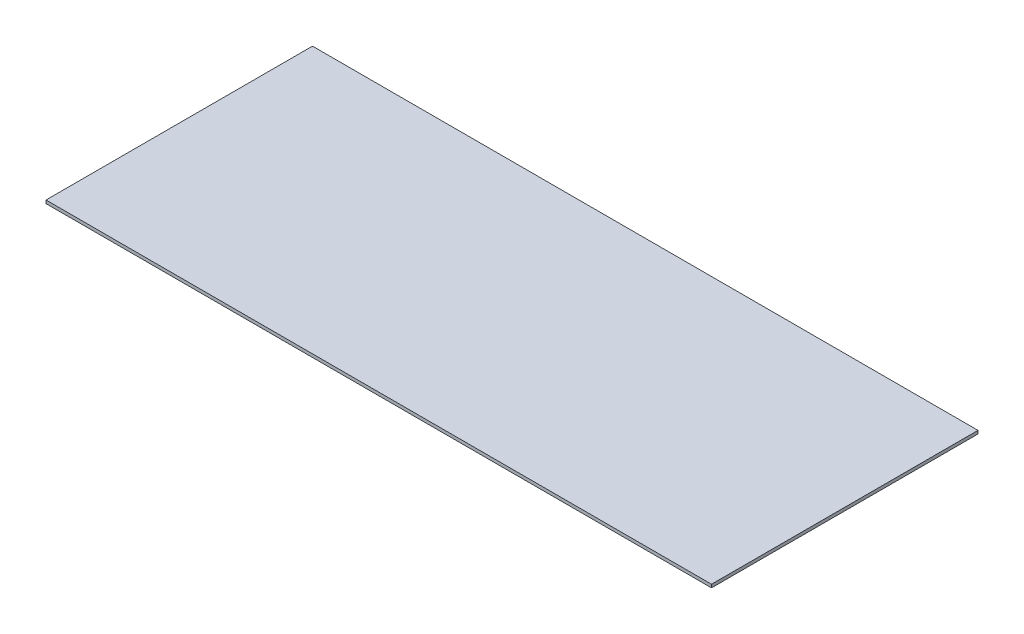
SolidWorks part; units mm, degrees
ref_plane "Front Plane" through (0, 0, 0) normal (0, 0, 1) x (1, 0, 0)
ref_plane "Top of Plywood" through (0, 0, 0) normal (0, 1, 0) x (1, 0, 0)
ref_plane "Right Plane" through (0, 0, 0) normal (1, 0, 0) x (0, 0, -1)
sketch "Interior Dim" plane through (0, 0, 0) normal (0, 1, 0) x (1, 0, 0)
  line L1 (0, 0) -> (5867.4, 0)
  line L2 (0, 0) -> (0, 2349.5)
  line L3 (0, 2349.5) -> (5867.4, 2349.5)
  line L4 (5867.4, 0) -> (5867.4, 2349.5)
  dimension "D1" = 5867.4
  dimension "D2" = 2349.5
sketch "Stud Centerlines" plane through (0, 0, 0) normal (0, 1, 0) x (1, 0, 0)
  line L0 (19.05, 19.05) -> (19.05, 2330.45) construction
  line L1 (19.05, 2330.45) -> (5867.4, 2330.45) construction
  line L2 (5867.4, 0) -> (5867.4, 2349.5) construction
  line L3 (5867.4, 19.05) -> (19.05, 19.05) construction
  line L4 (0, 0) -> (0, 2349.5) construction
  line L5 (0, 2349.5) -> (5867.4, 2349.5) construction
  line L6 (0, 0) -> (5867.4, 0) construction
  line L8 (4121.15, 2330.45) -> (4121.15, 19.05) construction
  line L9 (1771.65, 2330.45) -> (1771.65, 19.05) construction
  line L10 (19.05, 2051.05) -> (4121.15, 2051.05) construction
  dimension "D1" = 19.05
  dimension "D2" = 19.05
  dimension "D3" = 19.05
  dimension "D5" = 279.4
  dimension "D6" = 1752.6
  dimension "D7" = 2349.5
sketch "Gypsum Board" plane through (0, 0, 0) normal (0, 1, 0) x (1, 0, 0)
  line L0 (38.1, 38.1) -> (38.1, 2311.4)
  line L1 (38.1, 2311.4) -> (5867.4, 2311.4)
  line L2 (5867.4, 0) -> (5867.4, 2349.5) construction
  line L3 (50.8, 2298.7) -> (50.8, 50.8)
  line L4 (38.1, 38.1) -> (5867.4, 38.1)
  line L5 (50.8, 50.8) -> (5867.4, 50.8)
  line L6 (19.05, 19.05) -> (19.05, 2330.45) construction
  line L7 (19.05, 2330.45) -> (5867.4, 2330.45) construction
  line L8 (5867.4, 19.05) -> (19.05, 19.05) construction
  line L9 (4165.6, 50.8) -> (4165.6, 2095.5)
  line L10 (50.8, 2298.7) -> (5867.4, 2298.7)
  line L11 (4165.6, 2095.5) -> (4178.3, 2095.5)
  line L12 (4178.3, 2095.5) -> (4178.3, 50.8)
  line L13 (4121.15, 2330.45) -> (4121.15, 19.05) construction
  line L14 (19.05, 2051.05) -> (4121.15, 2051.05) construction
  line L15 (5867.4, 2311.4) -> (5867.4, 2298.7)
  line L16 (5867.4, 50.8) -> (5867.4, 38.1)
  line L17 (4165.6, 50.8) -> (4178.3, 50.8)
  dimension "D1" = 19.05
  dimension "D2" = 19.05
  dimension "D3" = 12.7
  dimension "D4" = 12.7
  dimension "D5" = 12.7
  dimension "D6" = 19.05
  dimension "D7" = 44.45
  dimension "D8" = 12.7
  dimension "D9" = 44.45
sketch "PVC" plane through (0, 0, 0) normal (0, 1, 0) x (1, 0, 0)
  line L0 (50.8, 50.8) -> (50.8, 2006.6)
  line L1 (4076.7, 50.8) -> (1841.5, 50.8)
  line L2 (50.8, 50.8) -> (1701.8, 50.8)
  line L3 (1701.8, 50.8) -> (1701.8, 2006.6)
  line L4 (1701.8, 2006.6) -> (50.8, 2006.6)
  line L5 (50.8, 2298.7) -> (50.8, 50.8) construction
  line L6 (19.05, 2051.05) -> (4121.15, 2051.05) construction
  line L7 (1771.65, 2330.45) -> (1771.65, 19.05) construction
  line L8 (50.8, 50.8) -> (5867.4, 50.8) construction
  line L9 (63.5, 1993.9) -> (1689.1, 1993.9)
  line L10 (1689.1, 1993.9) -> (1689.1, 63.5)
  line L11 (1689.1, 63.5) -> (63.5, 63.5)
  line L12 (63.5, 63.5) -> (63.5, 1993.9)
  line L13 (1841.5, 2006.6) -> (4076.7, 2006.6)
  line L14 (4076.7, 2006.6) -> (4076.7, 50.8)
  line L15 (1841.5, 50.8) -> (1841.5, 2006.6)
  line L16 (4121.15, 2330.45) -> (4121.15, 19.05) construction
  line L17 (1854.2, 1993.9) -> (1854.2, 63.5)
  line L18 (1854.2, 63.5) -> (4064, 63.5)
  line L19 (4064, 63.5) -> (4064, 1993.9)
  line L20 (4064, 1993.9) -> (1854.2, 1993.9)
  dimension "D1" = 0
  dimension "D2" = 44.45
  dimension "D3" = 69.85
  dimension "D4" = 0
  dimension "D5" = 12.7
  dimension "D6" = 12.7
  dimension "D7" = 12.7
  dimension "D8" = 12.7
  dimension "D9" = 69.85
  dimension "D10" = 44.45
  dimension "D11" = 12.7
  dimension "D12" = 12.7
  dimension "D13" = 12.7
  dimension "D14" = 12.7
sketch "Open Indoor Space" plane through (0, 0, 0) normal (0, 1, 0) x (1, 0, 0)
  line L0 (4178.3, 2095.5) -> (4165.6, 2095.5)
  line L1 (63.5, 63.5) -> (1689.1, 63.5)
  line L2 (63.5, 63.5) -> (63.5, 1993.9)
  line L3 (63.5, 1993.9) -> (1689.1, 1993.9)
  line L4 (1689.1, 63.5) -> (1689.1, 1993.9)
  line L5 (1854.2, 63.5) -> (4064, 63.5)
  line L6 (1854.2, 63.5) -> (1854.2, 1993.9)
  line L7 (1854.2, 1993.9) -> (4064, 1993.9)
  line L8 (4064, 63.5) -> (4064, 1993.9)
  line L9 (4165.6, 2095.5) -> (50.8, 2095.5)
  line L10 (50.8, 2298.7) -> (50.8, 50.8) construction
  line L11 (50.8, 2095.5) -> (50.8, 2298.7)
  line L12 (50.8, 2298.7) -> (5867.4, 2298.7)
  line L13 (5867.4, 2298.7) -> (5867.4, 50.8)
  line L14 (5867.4, 50.8) -> (4178.3, 50.8)
  line L15 (4178.3, 50.8) -> (4178.3, 2095.5)
ref_plane "Interior Roof" through (0, 2381.25, 0) normal (0, 1, 0) x (1, 0, 0)
ref_plane "Bottom of Plywood" through (0, -27.94, 0) normal (0, 1, 0) x (1, 0, 0)
sketch "Sketch4" plane through (0, 0, 0) normal (0, 1, 0) x (1, 0, 0)
  line L1 (0, 0) -> (5867.4, 0)
  line L2 (0, 0) -> (0, 2349.5)
  line L3 (0, 2349.5) -> (5867.4, 2349.5)
  line L4 (5867.4, 0) -> (5867.4, 2349.5)
extrude "Boss-Extrude2" add sketch "Sketch4" against normal up to surface (27.94 mm away) up to plane "Bottom of Plywood"
sketch "Sketch5" plane through (0, 0, 0) normal (0, 1, 0) x (1, 0, 0)
  line L0 (177.8, 63.5) -> (177.8, 0)
  line L1 (1689.1, 63.5) -> (63.5, 63.5) construction
  line L2 (0, 0) -> (5867.4, 0) construction
  line L3 (1168.4, 63.5) -> (1168.4, 0)
  line L4 (3022.6, 63.5) -> (3022.6, 0)
  line L5 (19.05, 19.05) -> (19.05, 2330.45) construction
  line L6 (1930.4, 63.5) -> (1930.4, 0)
  line L7 (1771.65, 2330.45) -> (1771.65, 19.05) construction
  dimension "D1" = 990.6
  dimension "D2" = 158.75
  dimension "D3" = 158.75
  dimension "D4" = 1092.2
ref_plane "Bottom of Roof Drywall" through (0, 2266.95, 0) normal (0, 1, 0) x (1, 0, 0)
ref_plane "Top of Insulated Subfloor" through (0, 40.64, 0) normal (0, 1, 0) x (1, 0, 0)
ref_plane "Top of Vinyl Flooring" through (0, 43.815, 0) normal (0, 1, 0) x (1, 0, 0)
sketch "Bathroom Floorspace" plane through (0, 0, 0) normal (0, 1, 0) x (1, 0, 0)
  line L1 (63.5, 1993.9) -> (1689.1, 1993.9)
  line L2 (63.5, 1993.9) -> (63.5, 63.5)
  line L3 (63.5, 63.5) -> (1689.1, 63.5)
  line L4 (1689.1, 1993.9) -> (1689.1, 63.5)
  line L5 (1854.2, 1993.9) -> (4064, 1993.9)
  line L6 (1854.2, 1993.9) -> (1854.2, 63.5)
  line L7 (1854.2, 63.5) -> (4064, 63.5)
  line L8 (4064, 1993.9) -> (4064, 63.5)
ref_plane "Top of Roof Drywall" through (0, 2279.65, 0) normal (0, 1, 0) x (1, 0, 0)
sketch "Drywall Roof Area" plane through (0, 0, 0) normal (0, 1, 0) x (1, 0, 0)
  line L0 (38.1, 38.1) -> (5867.4, 38.1) construction
  line L1 (38.1, 38.1) -> (1701.8, 38.1)
  line L2 (38.1, 38.1) -> (38.1, 2006.6)
  line L3 (38.1, 2006.6) -> (1701.8, 2006.6)
  line L4 (1701.8, 38.1) -> (1701.8, 2006.6)
  line L5 (4076.7, 2006.6) -> (1841.5, 2006.6)
  line L6 (4076.7, 2006.6) -> (4076.7, 38.1)
  line L7 (4076.7, 38.1) -> (1841.5, 38.1)
  line L8 (1841.5, 2006.6) -> (1841.5, 38.1)
  line L9 (5867.4, 38.1) -> (4165.6, 38.1)
  line L14 (4165.6, 2095.5) -> (4165.6, 38.1)
  line L19 (38.1, 2311.4) -> (5867.4, 2311.4)
  line L28 (5867.4, 2311.4) -> (5867.4, 38.1)
  line L29 (4165.6, 2095.5) -> (38.1, 2095.5)
  line L30 (38.1, 2095.5) -> (38.1, 2311.4)
ref_plane "Left Wall" through (0, 0, 0) normal (-1, 0, 0) x (0, 0, 1)
ref_plane "Back Wall" through (0, 0, -2349.5) normal (0, 0, -1) x (-1, 0, 0)
